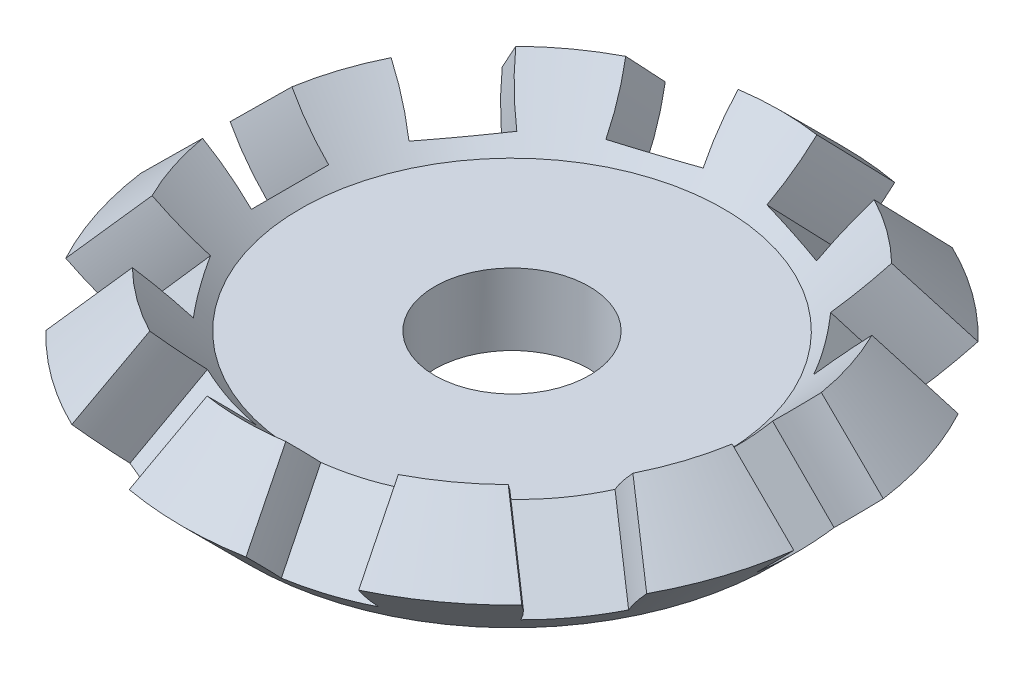
SolidWorks part; units mm, degrees
ref_plane "Front" through (0, 0, 0) normal (0, 0, 1) x (1, 0, 0)
ref_plane "Top" through (0, 0, 0) normal (0, 1, 0) x (1, 0, 0)
ref_plane "Right" through (0, 0, 0) normal (1, 0, 0) x (0, 0, -1)
sketch "Sketch2" plane through (0, 0, 0) normal (1, 0, 0) x (0, 0, -1)
  line L0 (0, 0) -> (-7.8982, 0)
  line L1 (-7.8982, 0) -> (-9.918, 2.0198)
  line L2 (-9.918, 2.0198) -> (-8.0783, 3.8595)
  line L3 (-8.0783, 3.8595) -> (-6.37, 2.1512)
  line L4 (-6.37, 2.1512) -> (0, 2.1512)
  line L5 (0, 55) -> (0, -55) construction
  line L6 (0, 2.1512) -> (0, 0)
  dimension "D1" = 7.8982
  dimension "D2" = 2.6018
  dimension "D3" = 2.4159
  dimension "D4" = 2.1512
  dimension "D5" = 45
revolve "Revolve2" add sketch "Sketch2" angle 360 about L6
sketch "Sketch3" plane through (0, 0, 0) normal (0, 0, 1) x (1, 0, 0)
  line L0 (0, 11.9379) -> (0, -7.011) construction
  line L1 (0, 11.9379) -> (-22.5767, -10.6389) construction
  line L2 (-8.0783, 3.8595) -> (-9.918, 2.0198) construction
ref_plane "Plane1" through (-3.9491, -3.9491, 0) normal (-0.7071, -0.7071, 0) x (0, 0, 1)
sketch "Sketch4" plane through (-3.9491, -3.9491, 0) normal (-0.7071, -0.7071, 0) x (0, 0, 1)
  line L0 (-1.1615, 6.5355) -> (1.1615, 6.5355)
  line L1 (0, 8.4413) -> (0, -4.9575) construction
  line L2 (3.7168, 12.9354) -> (-3.7168, 12.9354)
  line L3 (0, 24.746) -> (0, 11.4508) construction
  arc A0 (1.1615, 6.5355) -> (3.7168, 12.9354) centre (10.4535, 6.5355) cw
  arc A1 (-1.1615, 6.5355) -> (-3.7168, 12.9354) centre (-10.4535, 6.5355) ccw
  point P9 (0, 6.5355)
  point P12 (0, 12.9354)
  dimension "D2" = 9.292
  dimension "D1" = 1.1615
  dimension "D3" = 3.7168
extrude "Cut-Extrude1" cut sketch "Sketch4" against normal up to next
pattern_circular "CirPattern3" count 10 over 360 about axis through (0, 0, 0) along (0, 1, 0) of "Cut-Extrude1"
sketch "Sketch5" plane through (0, 2.1512, 0) normal (0, 1, 0) x (1, 0, 0)
  circle A0 centre (0, 0) radius 2.323
  dimension "D1" = 4.646
extrude "Cut-Extrude2" cut sketch "Sketch5" against normal up to next
